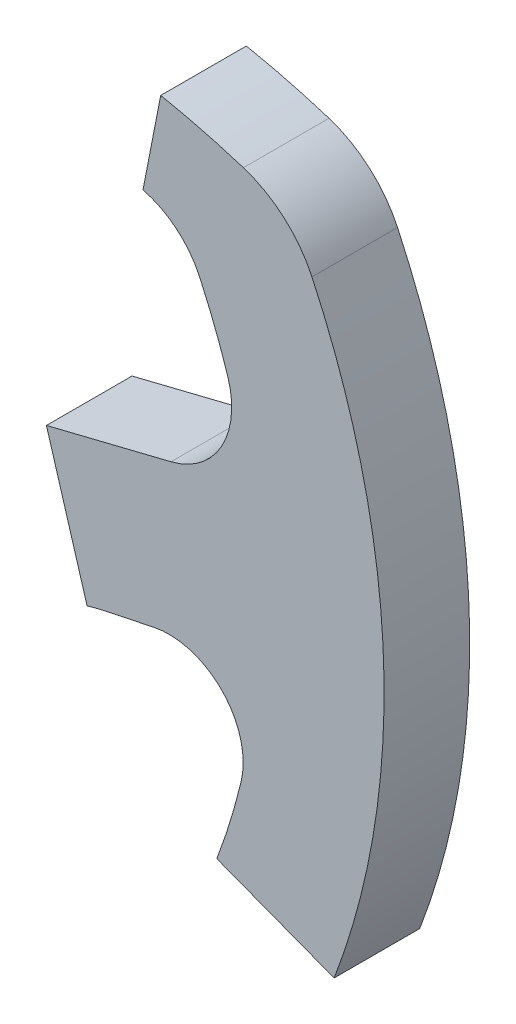
SolidWorks part; units mm, degrees
ref_plane "Płaszczyzna przednia" through (0, 0, 0) normal (0, 0, 1) x (1, 0, 0)
ref_plane "Płaszczyzna górna" through (0, 0, 0) normal (0, 1, 0) x (1, 0, 0)
ref_plane "Płaszczyzna prawa" through (0, 0, 0) normal (1, 0, 0) x (0, 0, -1)
sketch "Szkic1" plane through (0, 0, 0) normal (0, 0, 1) x (1, 0, 0)
  line L0 (-67.6782, 73.4513) -> (67.6782, 73.4513)
  arc A0 (-117.467, 64.4787) -> (-67.6782, 73.4513) centre (-70.3623, -54.2792) cw
  arc A1 (117.467, 64.4787) -> (67.6782, 73.4513) centre (70.3623, -54.2792) ccw
  line B0 (-96.6557, 16.4152) -> (-74.826, 11.0145)
  line B1 (-117.1447, 73.2126) -> (-117.2203, 65.4216)
  line B2 (117.2203, 65.4216) -> (117.1447, 73.2126)
  line B3 (0, -80.7783) -> (0, 58.8881) construction
  line B4 (-85.4268, -11.9367) -> (-93.6399, -10.216)
  line B5 (85.4268, -11.9367) -> (93.6399, -10.216)
  line B6 (96.6557, 16.4152) -> (74.826, 11.0145)
  circle B7 centre (-17.7108, 41.7394) radius 5
  circle B8 centre (0, 24.3225) radius 5
  circle B9 centre (17.7108, 41.7394) radius 5
  circle B10 centre (31.0909, 45.8177) radius 3.15
  circle B11 centre (-31.0909, 45.8177) radius 3.15
  circle B12 centre (-50, 24) radius 4.48
  circle B13 centre (-50, 24) radius 2.15
  circle B14 centre (-31.0909, 45.8177) radius 1.6
  circle B15 centre (31.0909, 45.8177) radius 1.6
  circle B16 centre (50, 24) radius 2.15
  circle B17 centre (50, 24) radius 4.48
  circle B18 centre (-50, -34) radius 2.15
  circle B19 centre (-50, -34) radius 4.48
  circle B20 centre (68.2878, -2.7328) radius 6.5
  circle B21 centre (47.1618, -18.7971) radius 5.5
  circle B22 centre (50, -34) radius 2.15
  arc B23 (-67.6782, 73.4513) -> (67.6782, 73.4513) centre (0, 223.4271) ccw
  arc B24 (-68.8555, 75.2743) -> (-67.6782, 73.4513) centre (-66.8555, 75.2743) ccw
  arc B25 (-68.853, 75.3756) -> (-68.8555, 75.2743) centre (-66.8555, 75.2743) ccw
  arc B26 (-116.7517, 74.3839) -> (-117.1447, 73.2126) centre (-115.1448, 73.1932) ccw
  arc B27 (-117.467, 64.4787) -> (-117.2203, 65.4216) centre (-119.2203, 65.4411) ccw
  arc B28 (-117.467, 64.4787) -> (-134, 0) centre (0, 0) ccw
  arc B29 (-134, 0) -> (-118.3736, -62.7988) centre (0, 0) ccw
  arc B30 (-118.3736, -62.7988) -> (-107.9536, -70.4995) centre (-105.1228, -55.7691) ccw
  arc B31 (-107.9536, -70.4995) -> (107.9536, -70.4995) centre (0, 491.259) ccw
  arc B32 (107.9536, -70.4995) -> (118.3736, -62.7988) centre (105.1228, -55.7691) ccw
  arc B33 (118.3736, -62.7988) -> (134, 0) centre (0, 0) ccw
  arc B34 (134, 0) -> (117.467, 64.4787) centre (0, 0) ccw
  arc B35 (117.2203, 65.4216) -> (117.467, 64.4787) centre (119.2203, 65.4411) ccw
  arc B36 (117.1447, 73.2126) -> (116.7517, 74.3839) centre (115.1448, 73.1932) ccw
  arc B37 (68.8555, 75.2743) -> (68.853, 75.3756) centre (66.8555, 75.2743) ccw
  arc B38 (67.6782, 73.4513) -> (68.8555, 75.2743) centre (66.8555, 75.2743) ccw
  circle B39 centre (50, -34) radius 4.48
  circle B40 centre (48.1712, -68.8185) radius 1.6
  circle B41 centre (48.1712, -68.8185) radius 3.15
  circle B42 centre (-48.1712, -68.8185) radius 1.6
  circle B43 centre (-48.1712, -68.8185) radius 3.15
  circle B44 centre (-68.2878, -2.7328) radius 6.5
  circle B45 centre (-47.1618, -18.7971) radius 5.5
  arc B46 (-101.6748, 46.9707) -> (-79.089, 52.7035) centre (-88.0576, 40.68) cw
  arc B47 (-107.2935, 30.0055) -> (-96.6557, 16.4152) centre (-93.2935, 30.0055) ccw
  arc B48 (-74.826, 11.0145) -> (-58.5214, 15.2443) centre (-70.5787, 28.1823) ccw
  arc B49 (-79.089, 52.7035) -> (-72.4785, 48.5874) centre (-51.3325, 89.9146) ccw
  arc B50 (-56.809, 31.3107) -> (-72.4785, 48.5874) centre (-87.5102, 19.2097) ccw
  arc B51 (-106.6211, 34.292) -> (-107.2935, 30.0055) centre (-93.2935, 30.0055) ccw
  arc B52 (-101.6748, 46.9707) -> (-106.6211, 34.292) centre (0, 0) ccw
  arc B53 (-109.3056, -22.9397) -> (-108.9518, -25.952) centre (-96.3056, -22.9397) ccw
  arc B54 (-108.9518, -25.952) -> (-104.6833, -39.8171) centre (0, 0) ccw
  arc B55 (-104.6833, -39.8171) -> (-95.5636, -47.3664) centre (-93.4673, -35.551) ccw
  arc B56 (-95.5636, -47.3664) -> (-72.2851, -50.9814) centre (0, 491.259) ccw
  arc B57 (-57.2278, -32.3367) -> (-85.4268, -11.9367) centre (-94.1826, -53.7295) ccw
  arc B58 (-93.6399, -10.216) -> (-109.3056, -22.9397) centre (-96.3056, -22.9397) ccw
  arc B59 (93.6399, -10.216) -> (109.3056, -22.9397) centre (96.3056, -22.9397) cw
  arc B60 (57.2278, -32.3367) -> (85.4268, -11.9367) centre (94.1826, -53.7295) cw
  arc B61 (95.5636, -47.3664) -> (72.2851, -50.9814) centre (0, 491.259) cw
  arc B62 (104.6833, -39.8171) -> (95.5636, -47.3664) centre (93.4673, -35.551) cw
  arc B63 (108.9518, -25.952) -> (104.6833, -39.8171) centre (0, 0) cw
  arc B64 (109.3056, -22.9397) -> (108.9518, -25.952) centre (96.3056, -22.9397) cw
  arc B65 (107.2935, 30.0055) -> (96.6557, 16.4152) centre (93.2935, 30.0055) cw
  arc B66 (106.6211, 34.292) -> (107.2935, 30.0055) centre (93.2935, 30.0055) cw
  arc B67 (101.6748, 46.9707) -> (106.6211, 34.292) centre (0, 0) cw
  arc B68 (101.6748, 46.9707) -> (79.089, 52.7035) centre (88.0576, 40.68) ccw
  arc B69 (79.089, 52.7035) -> (72.4785, 48.5874) centre (51.3325, 89.9146) cw
  arc B70 (56.809, 31.3107) -> (72.4785, 48.5874) centre (87.5102, 19.2097) cw
  arc B71 (74.826, 11.0145) -> (58.5214, 15.2443) centre (70.5787, 28.1823) cw
  circle B72 centre (-107.7383, -56.2792) radius 5
  circle B73 centre (-88.0461, -59.7886) radius 5
  circle B74 centre (-68.1859, -62.5968) radius 5
  circle B75 centre (68.1859, -62.5968) radius 5
  circle B76 centre (88.0461, -59.7886) radius 5
  circle B77 centre (107.7383, -56.2792) radius 5
  spline B78 degree 3 poles (-58.5214, 15.2443) (-55.1631, 18.3739) (-54.6835, 25.9182) (-56.809, 31.3107) knots 0 0 0 0 1 1 1 1 weights 1 1 1 1
  spline B79 degree 3 poles (-68.853, 75.3756) (-68.8507, 75.42) (-68.8464, 75.6195) (-68.9035, 76.1544) (-69.336, 77.2204) (-70.7194, 78.9099) (-73.024, 80.8304) (-77.2436, 83.4705) (-84.3742, 86.4487) (-94.38, 87.9189) (-104.0869, 86.0486) (-110.9538, 81.3247) (-114.8579, 76.8819) (-116.3512, 74.924) (-116.7407, 74.3987) (-116.7517, 74.3839) knots 0.039986 0.039986 0.039986 0.039986 0.049001 0.080251 0.142751 0.205251 0.267751 0.330251 0.455251 0.580251 0.705251 0.830251 0.892751 0.914629 0.915265 0.915265 0.915265 0.915265 weights 1 1 1 1 1 1 1 1 1 1 1 1 1 1 1 1
  spline B80 degree 3 poles (116.7517, 74.3839) (116.7407, 74.3987) (116.3512, 74.924) (114.8579, 76.8819) (110.9538, 81.3247) (104.0869, 86.0486) (94.38, 87.9189) (84.3742, 86.4487) (77.2436, 83.4705) (73.024, 80.8304) (70.7194, 78.9099) (69.336, 77.2204) (68.9035, 76.1544) (68.8464, 75.6195) (68.8507, 75.42) (68.853, 75.3756) knots 0.039986 0.039986 0.039986 0.039986 0.040622 0.0625 0.125 0.25 0.375 0.5 0.625 0.6875 0.75 0.8125 0.875 0.90625 0.915265 0.915265 0.915265 0.915265 weights 1 1 1 1 1 1 1 1 1 1 1 1 1 1 1 1
  spline B81 degree 3 poles (-72.2851, -50.9814) (-64.3666, -52.037) (-50.3887, -44.1509) (-57.2278, -32.3367) knots 0 0 0 0 1 1 1 1 weights 1 1 1 1
  spline B82 degree 3 poles (72.2851, -50.9814) (64.3666, -52.037) (50.3887, -44.1509) (57.2278, -32.3367) knots 0 0 0 0 1 1 1 1 weights 1 1 1 1
  spline B83 degree 3 poles (58.5214, 15.2443) (55.1631, 18.3739) (54.6835, 25.9182) (56.809, 31.3107) knots 0 0 0 0 1 1 1 1 weights 1 1 1 1
sketch_block_instance "Blok-rdzen-1"
sketch_block "Blok-rdzen"
sketch "Szkic2" plane through (0, 0, 0) normal (0, 0, -1) x (-1, 0, 0)
  line L0 (-74.826, 11.0145) -> (-81.9514, -12.8186)
  line L1 (-104.6833, -39.8171) -> (-125.2461, -47.6383)
  line L2 (-91.7479, 55.2189) -> (-94.8516, 71.1104)
  line L3 (-96.6557, 16.4152) -> (-74.826, 11.0145) construction
  line L4 (-85.4268, -11.9367) -> (-93.6399, -10.216) construction
  line L5 (-96.6557, 16.4152) -> (-74.826, 11.0145)
  line L6 (-85.4268, -11.9367) -> (-93.6399, -10.216)
  arc A1 (-121.3563, 56.8211) -> (-118.3736, -62.7988) centre (0, 0) ccw construction
  arc A2 (-79.089, 52.7035) -> (-101.6748, 46.9707) centre (-88.0576, 40.68) ccw construction
  arc A3 (-67.6782, 73.4513) -> (-109.3462, 67.3865) centre (-70.3623, -54.2792) ccw construction
  arc A4 (-109.3462, 67.3865) -> (-121.3563, 56.8211) centre (-103.2435, 48.3403) ccw construction
  arc A5 (-101.6748, 46.9707) -> (-106.6211, 34.292) centre (0, 0) ccw construction
  arc A6 (-106.6211, 34.292) -> (-96.6557, 16.4152) centre (-93.2935, 30.0055) ccw construction
  arc A7 (-93.6399, -10.216) -> (-108.9518, -25.952) centre (-96.3056, -22.9397) ccw construction
  arc A8 (-108.9518, -25.952) -> (-104.6833, -39.8171) centre (0, 0) ccw construction
  arc A9 (-109.3462, 67.3865) -> (-121.3563, 56.8211) centre (-103.2435, 48.3403) ccw
  arc A10 (-101.6748, 46.9707) -> (-106.6211, 34.292) centre (0, 0) ccw
  arc A11 (-106.6211, 34.292) -> (-96.6557, 16.4152) centre (-93.2935, 30.0055) ccw
  arc A12 (-93.6399, -10.216) -> (-108.9518, -25.952) centre (-96.3056, -22.9397) ccw
  arc A13 (-108.9518, -25.952) -> (-104.6833, -39.8171) centre (0, 0) ccw
  arc A14 (-125.2461, -47.6383) -> (-121.3563, 56.8211) centre (0, 0) cw
  arc A15 (-91.7479, 55.2189) -> (-101.6748, 46.9707) centre (-88.0576, 40.68) ccw
  arc A16 (-94.8516, 71.1104) -> (-109.3462, 67.3865) centre (-70.3623, -54.2792) ccw
  arc A17 (-57.2278, -32.3367) -> (-85.4268, -11.9367) centre (-94.1826, -53.7295) ccw construction
  arc A18 (-81.9514, -12.8186) -> (-85.4268, -11.9367) centre (-94.1826, -53.7295) ccw
sketch "Szkic3" plane through (71.7094, 21.439, 0) normal (-0.9581, -0.2864, 0) x (0, 0, 1)
  line L0 (0, -35.7558) -> (0, -10.8804)
  arc A0 (0, -35.7558) -> (0, -10.8804) centre (12.0369, -23.3181) cw
  spline S0 degree 1 poles (0, -35.7558) (0, -10.8804) knots 0 0 1 1
ref_plane "Płaszczyzna1" through (81.2904, 24.3034, 0) normal (-0.9581, -0.2864, 0) x (0, 0, 1)
sketch "Szkic4" plane through (81.2904, 24.3034, 0) normal (-0.9581, -0.2864, 0) x (0, 0, 1)
  line L0 (0, -35.7558) -> (0, -10.8804)
  arc A1 (0, -35.7558) -> (0, -10.8804) centre (5.4867, -23.3181) cw
ref_plane "Płaszczyzna2" through (90.8714, 27.1678, 0) normal (-0.9581, -0.2864, 0) x (0, 0, 1)
sketch "Szkic6" plane through (90.8714, 27.1678, 0) normal (-0.9581, -0.2864, 0) x (0, 0, 1)
  circle A0 centre (-9.3078, -23.7871) radius 28.4591
sketch "Szkic7" plane through (90.8714, 27.1678, 0) normal (0.9581, 0.2864, 0) x (0, 0, -1)
  line L0 (0, -40.3264) -> (0, -11.8407)
  arc A0 (0, -11.8407) -> (0, -40.3264) centre (-3.304, -26.0836) cw
sketch "Szkic9" plane through (0, 0, -16) normal (0, 0, -1) x (-1, 0, 0)
  line L0 (-109.2651, -21.9141) -> (-105.6735, 23.4683)
  arc A0 (-93.6399, -10.216) -> (-109.3056, -22.9397) centre (-96.3056, -22.9397) ccw construction
  arc A1 (-107.2935, 30.0055) -> (-96.6557, 16.4152) centre (-93.2935, 30.0055) ccw construction
ref_plane "Płaszczyzna3" through (106.8615, 8.4571, 0) normal (0.9969, 0.0789, 0) x (-0.0789, 0.9969, 0)
sketch "Szkic10" plane through (106.8615, 8.4571, 0) normal (0.9969, 0.0789, 0) x (-0.0789, 0.9969, 0)
  circle A0 centre (0, -13.0274) radius 152.4648
sketch "Szkic11" plane through (106.8615, 8.4571, 0) normal (0.9969, 0.0789, 0) x (0, 0, -1)
  line L0 (0, -30.4661) -> (16, -30.4661) construction
  line L1 (0, 15.0582) -> (0, -30.4661) construction
  line L2 (0, 15.0582) -> (0, -30.4661)
  arc A0 (0, 15.0582) -> (0, -30.4661) centre (-11.4434, -7.704) cw
sketch "Szkic13" plane through (0, 0, 0) normal (0, 0, 1) x (1, 0, 0)
  line L0 (105.6735, 23.4683) -> (109.2651, -21.9141)
  line L1 (91.7479, 55.2189) -> (94.8516, 71.1104) construction
  line L2 (104.6833, -39.8171) -> (125.2461, -47.6383) construction
  line L3 (91.7479, 55.2189) -> (94.8516, 71.1104)
  line L4 (104.6833, -39.8171) -> (125.2461, -47.6383)
  arc A0 (109.2651, -21.9141) -> (109.3056, -22.9397) centre (96.3056, -22.9397) cw
  arc A1 (96.6557, 16.4152) -> (107.2935, 30.0055) centre (93.2935, 30.0055) ccw construction
  arc A2 (107.2935, 30.0055) -> (106.6211, 34.292) centre (93.2935, 30.0055) ccw construction
  arc A3 (106.6211, 34.292) -> (101.6748, 46.9707) centre (0, 0) ccw construction
  arc A6 (121.3563, 56.8211) -> (109.3462, 67.3865) centre (103.2435, 48.3403) ccw construction
  arc A8 (118.3736, -62.7988) -> (134, 0) centre (0, 0) ccw construction
  arc A9 (104.6833, -39.8171) -> (108.9518, -25.952) centre (0, 0) ccw construction
  arc A10 (108.9518, -25.952) -> (109.3056, -22.9397) centre (96.3056, -22.9397) ccw construction
  arc A11 (96.6557, 16.4152) -> (107.2935, 30.0055) centre (93.2935, 30.0055) ccw
  arc A12 (107.2935, 30.0055) -> (106.6211, 34.292) centre (93.2935, 30.0055) ccw
  arc A13 (106.6211, 34.292) -> (101.6748, 46.9707) centre (0, 0) ccw
  arc A14 (91.7479, 55.2189) -> (101.6748, 46.9707) centre (88.0576, 40.68) cw
  arc A15 (94.8516, 71.1104) -> (109.3462, 67.3865) centre (70.3623, -54.2792) cw
  arc A16 (121.3563, 56.8211) -> (109.3462, 67.3865) centre (103.2435, 48.3403) ccw
  arc A17 (134, 0) -> (121.3563, 56.8211) centre (0, 0) ccw
  arc A18 (125.2461, -47.6383) -> (134, 0) centre (0, 0) ccw
  arc A19 (104.6833, -39.8171) -> (108.9518, -25.952) centre (0, 0) ccw
  arc A20 (108.9518, -25.952) -> (109.3056, -22.9397) centre (96.3056, -22.9397) ccw
extrude "Dodanie-wyciągnięcie1" add sketch "Szkic2" along normal blind 15
